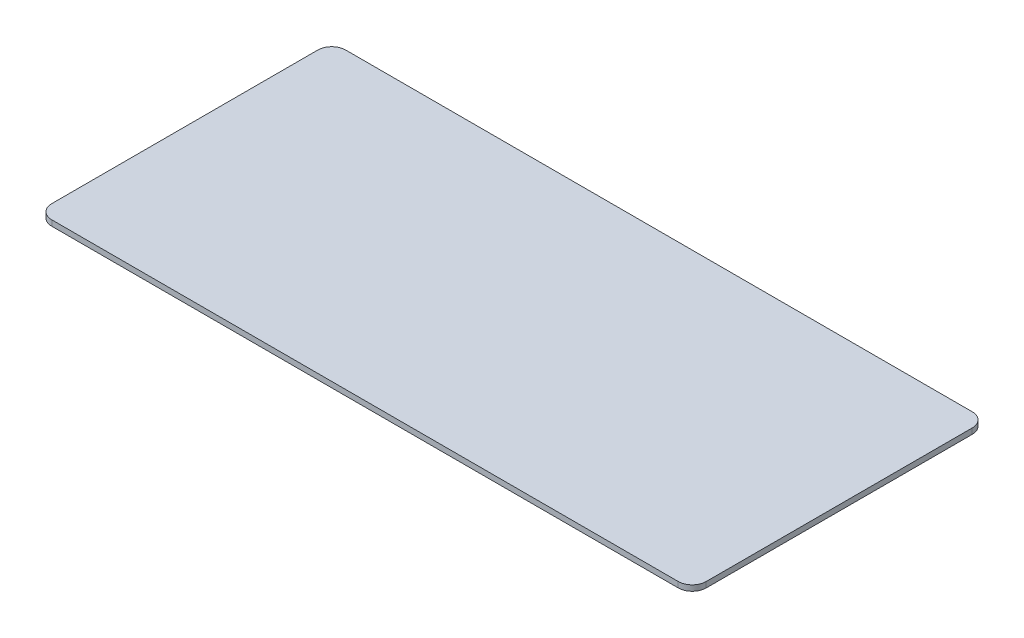
SolidWorks part; units mm, degrees
ref_plane "前视基准面" through (0, 0, 0) normal (0, 0, 1) x (1, 0, 0)
ref_plane "上视基准面" through (0, 0, 0) normal (0, 1, 0) x (1, 0, 0)
ref_plane "右视基准面" through (0, 0, 0) normal (1, 0, 0) x (0, 0, -1)
other "Configuration Table"
sketch "草图1" plane through (0, 0, 0) normal (0, 1, 0) x (1, 0, 0)
  line L1 (-71.3431, -35.0601) -> (18.1569, -35.0601)
  line L2 (-73.3431, -33.0601) -> (-73.3431, 4.9399)
  line L3 (-71.3431, 6.9399) -> (18.1569, 6.9399)
  line L4 (20.1569, -33.0601) -> (20.1569, 4.9399)
  line L5 (-73.3431, -35.0601) -> (20.1569, 6.9399) construction
  line L6 (-73.3431, 6.9399) -> (20.1569, -35.0601) construction
  arc A0 (18.1569, -35.0601) -> (20.1569, -33.0601) centre (18.1569, -33.0601) ccw
  arc A1 (-73.3431, 4.9399) -> (-71.3431, 6.9399) centre (-71.3431, 4.9399) cw
  arc A2 (-71.3431, -35.0601) -> (-73.3431, -33.0601) centre (-71.3431, -33.0601) cw
  arc A3 (18.1569, 6.9399) -> (20.1569, 4.9399) centre (18.1569, 4.9399) cw
  point P0 (-26.5931, -14.0601)
  point P6 (0, 0)
  point P7 (-28.7083, -13.7167)
  point P8 (20.6569, -35.3302)
  point P9 (-73.3431, 7.0071)
  dimension "D3" = 2
  dimension "D1" = 93.5
  dimension "D2" = 42
extrude "凸台-拉伸1" add sketch "草图1" along normal blind 0.8
